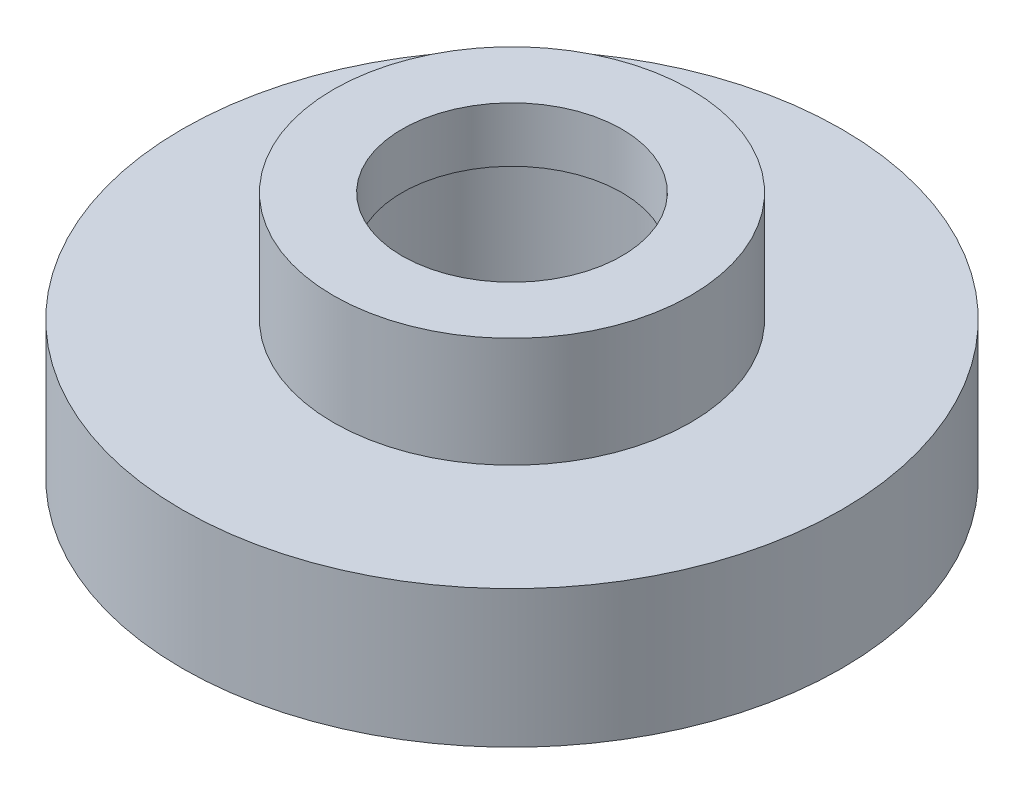
SolidWorks part; units mm, degrees
ref_plane "Front Plane" through (0, 0, 0) normal (0, 0, 1) x (1, 0, 0)
ref_plane "Top Plane" through (0, 0, 0) normal (0, 1, 0) x (1, 0, 0)
ref_plane "Right Plane" through (0, 0, 0) normal (1, 0, 0) x (0, 0, -1)
sketch "Sketch1" plane through (0, 0, 0) normal (0, 1, 0) x (1, 0, 0)
  circle A0 centre (0, 0) radius 12
  dimension "D1" = 24
extrude "Boss-Extrude1" add sketch "Sketch1" along normal blind 5
sketch "Sketch2" plane through (0, 5, 0) normal (0, 1, 0) x (1, 0, 0)
  circle A0 centre (0, 0) radius 6.5
  dimension "D1" = 13
extrude "Boss-Extrude2" add sketch "Sketch2" along normal blind 4
sketch "Sketch3" plane through (0, 0, 0) normal (0, -1, 0) x (1, 0, 0)
  circle A0 centre (0, 0) radius 5.1
  dimension "D1" = 10.2
extrude "Cut-Extrude1" cut sketch "Sketch3" against normal blind 7
sketch "Sketch4" plane through (0, 9, 0) normal (0, 1, 0) x (1, 0, 0)
  circle A0 centre (0, 0) radius 4
  dimension "D1" = 8
extrude "Cut-Extrude2" cut sketch "Sketch4" against normal blind 7
